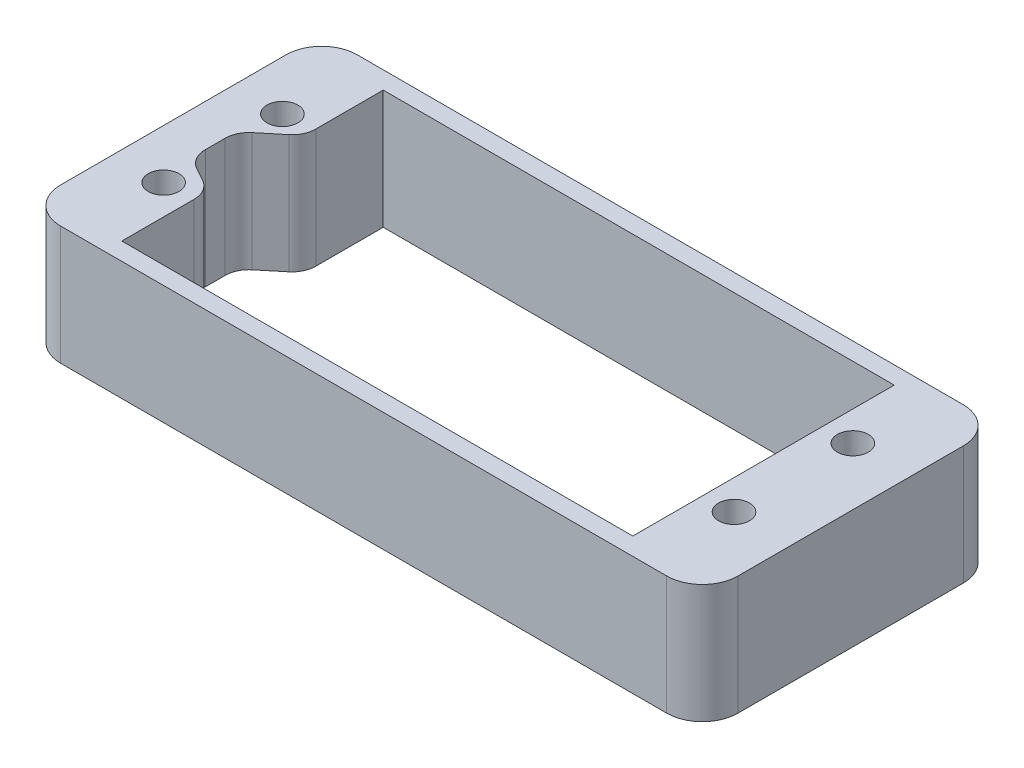
SolidWorks part; units mm, degrees
ref_plane "Alzado" through (0, 0, 0) normal (0, 0, 1) x (1, 0, 0)
ref_plane "Planta" through (0, 0, 0) normal (0, 1, 0) x (1, 0, 0)
ref_plane "Vista lateral" through (0, 0, 0) normal (1, 0, 0) x (0, 0, -1)
sketch "Croquis1" plane through (0, 0, 0) normal (0, 1, 0) x (1, 0, 0)
  line L0 (-10.6555, 24.4303) -> (32.3445, 24.4303)
  line L1 (-10.6555, 24.4303) -> (-10.6555, 2.4303)
  line L2 (-10.6555, 2.4303) -> (32.3445, 2.4303)
  line L3 (32.3445, 24.4303) -> (32.3445, 2.4303)
  line L4 (-17.318, 25.908) -> (39.682, 25.908)
  line L5 (-17.318, 25.908) -> (-17.318, 0.9485)
  line L6 (-17.318, 0.9485) -> (39.682, 0.9485)
  line L7 (39.682, 25.908) -> (39.682, 0.9485)
  dimension "D1" = 43
  dimension "D2" = 22
extrude "Main" add sketch "Croquis1" along normal blind 28
sketch "Croquis2" plane through (0, 0, -0.9485) normal (0, 0, 1) x (1, 0, 0)
  line L0 (-17.318, 28) -> (-17.318, 0) construction
  line L1 (14.682, 30.988) -> (42.6379, 30.988)
  line L2 (14.682, 30.988) -> (14.682, 10)
  line L3 (14.682, 10) -> (42.6379, 10)
  line L4 (42.6379, 30.988) -> (42.6379, 10)
  line L5 (-17.318, 0) -> (39.682, 0) construction
  dimension "D1" = 32
  dimension "D2" = 10
extrude "Corte Caja " cut sketch "Croquis2" against normal up to surface (24.9595 mm away) up to face at (11.182, 14, -25.908)
sketch "Croquis3" plane through (0, 28, 0) normal (0, 1, 0) x (1, 0, 0)
  line L0 (39.682, 25.908) -> (14.682, 25.908) construction
  line L1 (14.682, 25.908) -> (-17.318, 25.908)
  line L2 (14.682, 25.908) -> (14.682, 0.9485)
  line L3 (14.682, 0.9485) -> (-17.318, 0.9485)
  line L4 (-17.318, 25.908) -> (-17.318, 0.9485) construction
  line L6 (16.029, 25.908) -> (26.5297, 25.908) construction
  line L7 (16.029, 24.4303) -> (26.5297, 24.4303) construction
  line L8 (14.682, 24.4303) -> (32.3445, 24.4303) construction
  line L9 (-17.318, 25.908) -> (-17.318, 0.9485)
extrude "Saliente-Extruir2" add sketch "Croquis3" along normal blind 2.25
fillet "Redondeo Laterales" radius 3 4 edges at (-17.318, 15.125, -25.908) (-17.318, 15.125, -0.9485) (39.682, 5, -25.908) (39.682, 5, -0.9485)
sketch "Croquis7" plane through (0, 0, 0) normal (0, -1, 0) x (1, 0, 0)
  line L0 (-18.892, -13.4485) -> (40.144, -13.4485) construction
  line L1 (-18.892, -8.4485) -> (40.144, -8.4485) construction
  line L2 (-18.892, -18.4485) -> (40.6935, -18.4485) construction
  line L3 (-18.2815, -24.4303) -> (39.5335, -24.4303) construction
  line L5 (-13.1555, 4.5429) -> (-13.1555, -27.3866) construction
  line L6 (39.7888, 0) -> (39.7888, -27.3866) construction
  line L7 (32.3445, -2.4303) -> (32.3445, -24.4303) construction
  line L8 (34.8445, 2.284) -> (34.8445, -29.5844) construction
  line L9 (-10.6555, -24.4303) -> (-10.6555, -2.4303) construction
  line L10 (-14.318, -0.9485) -> (36.682, -0.9485) construction
  line L11 (36.682, -25.908) -> (-14.318, -25.908) construction
  circle A0 centre (-13.1555, -8.4485) radius 1.3
  circle A1 centre (-13.1555, -18.4485) radius 1.3
  circle A2 centre (34.8445, -8.4485) radius 1.3
  circle A3 centre (34.8445, -18.4485) radius 1.3
  dimension "D7" = 12.4595
  dimension "D1" = 12.5
  dimension "D2" = 5
  dimension "D3" = 5
  dimension "D4" = 7.4443
  dimension "D5" = 2.5
  dimension "D6" = 2.5
  dimension "D8" = 48
extrude "Taladros Base" cut sketch "Croquis7" against normal blind 11
sketch "Croquis8" plane through (0, 0, 0) normal (0, -1, 0) x (1, 0, 0)
  line L0 (-21.6745, -13.4485) -> (6.4227, -13.4485) construction
  line L1 (-10.6555, -24.4303) -> (-10.6555, -2.4303) construction
  line L2 (-10.6555, -17.8094) -> (-10.6555, -9.6935)
  line L3 (-13.7999, -11.4172) -> (-13.7999, -15.2167)
  line L4 (-13.7999, -15.2167) -> (-10.6555, -17.8094)
  line L5 (-13.7999, -11.4172) -> (-10.6555, -9.6935)
  line L6 (-14.318, -0.9485) -> (36.682, -0.9485) construction
  line L7 (-10.6555, -24.4303) -> (-10.6555, -2.4303) construction
  dimension "D1" = 12.5
extrude "Cajeado cable" cut sketch "Croquis8" against normal blind 10
fillet "Cajeado Redondeo" radius 2 4 edges at (-10.6555, 5, -17.8094) (-13.7999, 5, -15.2167) (-13.7999, 5, -11.4172) (-10.6555, 5, -9.6935)
sketch "Croquis10" plane through (0, 0, -0.9485) normal (0, 0, 1) x (1, 0, 0)
  line L1 (14.682, 10) -> (36.682, 10) construction
  line L2 (-18.7514, 10) -> (41.2523, 10)
  line L3 (41.2523, 10) -> (41.2523, 38.9045)
  line L4 (41.2523, 38.9045) -> (-18.7514, 38.9045)
  line L5 (-18.7514, 38.8986) -> (-18.7514, 10)
  line L6 (-18.7514, 38.8986) -> (-18.7514, 38.9045)
extrude "Cortar-Extruir1" cut sketch "Croquis10" against normal up to surface (24.9595 mm away) up to face at (12.3487, 13.4167, -25.908)
